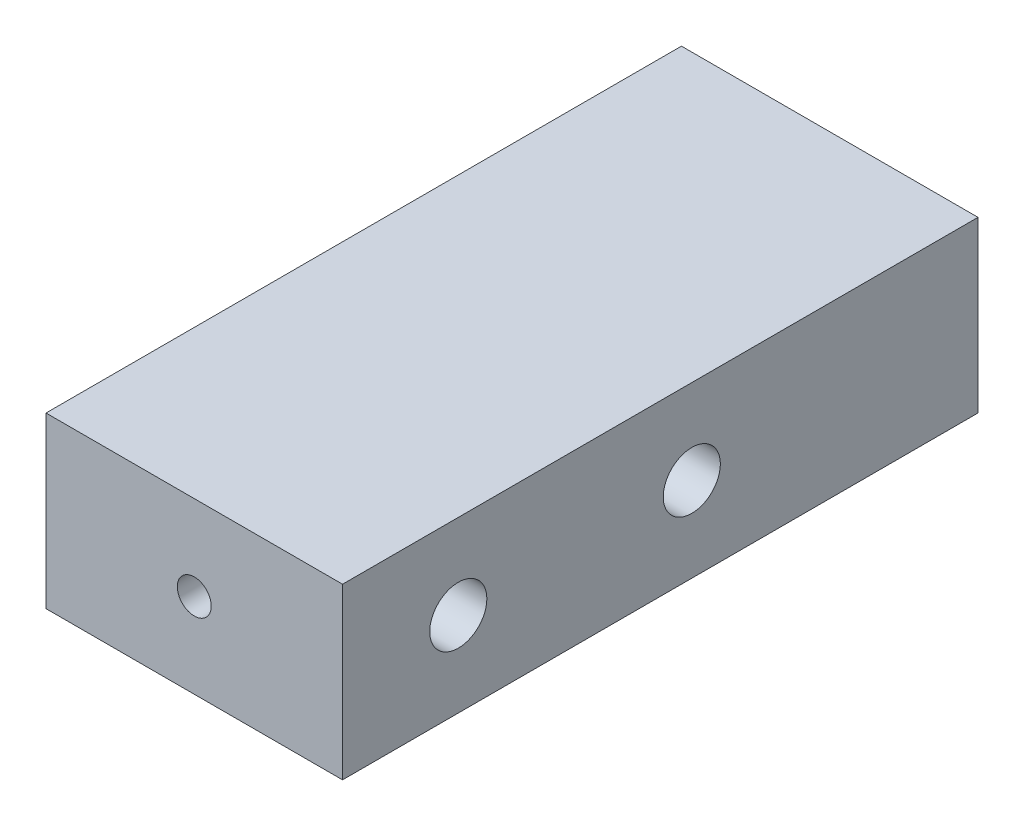
SolidWorks part; units mm, degrees
ref_plane "Front Plane" through (0, 0, 0) normal (0, 0, 1) x (1, 0, 0)
ref_plane "Top Plane" through (0, 0, 0) normal (0, 1, 0) x (1, 0, 0)
ref_plane "Right Plane" through (0, 0, 0) normal (1, 0, 0) x (0, 0, -1)
sketch "Sketch1" plane through (0, 0, 0) normal (0, 0, 1) x (1, 0, 0)
  line L1 (0, 25.4) -> (44.45, 25.4)
  line L2 (0, 25.4) -> (0, 0)
  line L3 (0, 0) -> (44.45, 0)
  line L4 (44.45, 25.4) -> (44.45, 0)
  dimension "D1" = 25.4
  dimension "D2" = 44.45
extrude "Boss-Extrude1" add sketch "Sketch1" along normal blind 95.25
sketch "Sketch2" plane through (0, 0, 0) normal (-1, 0, 0) x (0, 0, 1)
  line L0 (0, 25.4) -> (0, 0) construction
  line L1 (0, 12.7) -> (95.25, 12.7) construction
  line L2 (95.25, 25.4) -> (95.25, 0) construction
  circle A0 centre (25.4, 12.7) radius 4.28
  circle A1 centre (60.4, 12.7) radius 4.28
  dimension "D2" = 8.56
  dimension "D1" = 35
  dimension "D3" = 25.4
extrude "Cut-Extrude1" cut sketch "Sketch2" against normal blind 14.224
sketch "Sketch3" plane through (44.45, 0, 0) normal (1, 0, 0) x (0, 0, -1)
  line L0 (0, 12.7) -> (-95.25, 12.7) construction
  line L1 (0, 0) -> (0, 25.4) construction
  line L2 (-95.25, 0) -> (-95.25, 25.4) construction
  circle A0 centre (-77.9, 12.7) radius 4.28
  circle A1 centre (-42.9, 12.7) radius 4.28
  circle A2 centre (-25.4, 12.7) radius 4.28 construction
  dimension "D1" = 8.56
  dimension "D2" = 35
  dimension "D3" = 17.5
extrude "Cut-Extrude2" cut sketch "Sketch3" against normal blind 14.224
sketch "Sketch5" plane through (0, 0, 0) normal (0, 0, -1) x (-1, 0, 0)
  line L0 (-44.45, 25.4) -> (0, 0) construction
  line L1 (-44.45, 0) -> (-44.45, 25.4) construction
  line L2 (-44.45, 25.4) -> (0, 25.4) construction
  circle A0 centre (-22.225, 12.7) radius 4.2799
  dimension "D1" = 8.5598
extrude "Cut-Extrude4" cut sketch "Sketch5" against normal blind 14.224
sketch "Sketch6" plane through (0, 0, 14.224) normal (0, 0, -1) x (-1, 0, 0)
  circle A0 centre (-22.225, 12.7) radius 2.54
  circle A1 centre (-22.225, 12.7) radius 4.2799 construction
  point P2 (-20.9311, 8.0325)
  dimension "D1" = 5.08
extrude "Cut-Extrude5" cut sketch "Sketch6" against normal blind 86.36
sketch "Sketch7" plane through (30.226, 0, 0) normal (1, 0, 0) x (0, 0, -1)
  circle A0 centre (-42.9, 12.7) radius 2.54
  circle A1 centre (-77.9, 12.7) radius 2.54
  dimension "D1" = 5.08
extrude "Cut-Extrude6" cut sketch "Sketch7" against normal up to surface (5.461 mm away) up to face at (24.765, 12.7, 95.25)
sketch "Sketch8" plane through (14.224, 0, 0) normal (-1, 0, 0) x (0, 0, 1)
  circle A0 centre (25.4, 12.7) radius 2.54
  circle A1 centre (60.4, 12.7) radius 2.54
  dimension "D1" = 5.08
extrude "Cut-Extrude7" cut sketch "Sketch8" against normal up to surface (8.001 mm away)
